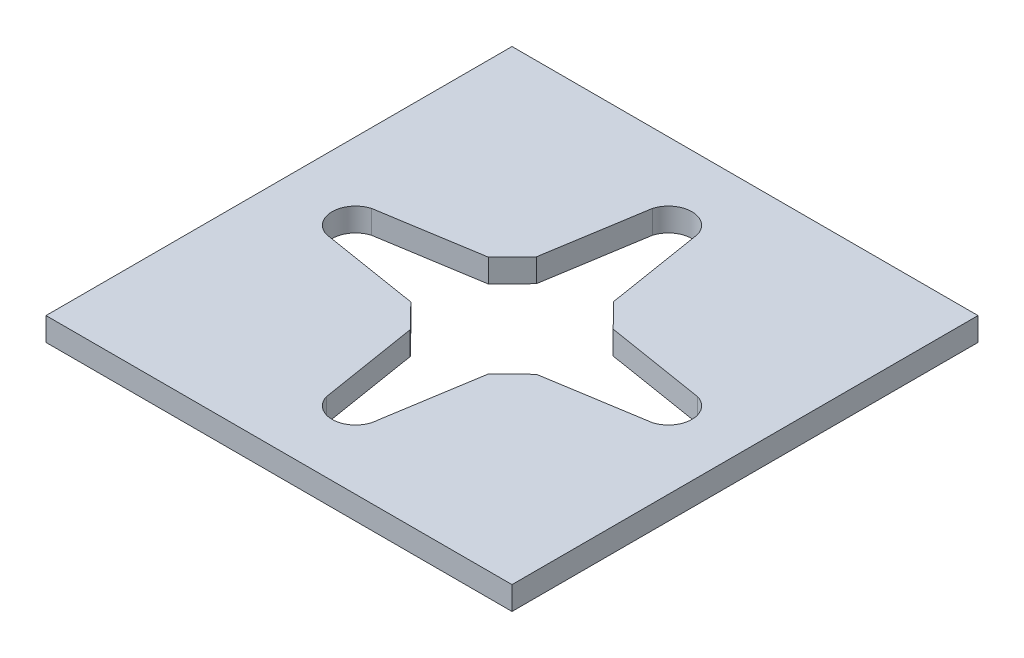
SolidWorks part; units mm, degrees
ref_plane "Front Plane" through (0, 0, 0) normal (0, 0, 1) x (1, 0, 0)
ref_plane "Top Plane" through (0, 0, 0) normal (0, 1, 0) x (1, 0, 0)
ref_plane "Right Plane" through (0, 0, 0) normal (1, 0, 0) x (0, 0, -1)
sketch "Sketch1" plane through (0, 0, 0) normal (0, 1, 0) x (1, 0, 0)
  line L1 (-25.4, -25.4) -> (25.4, -25.4)
  line L2 (-25.4, -25.4) -> (-25.4, 25.4)
  line L3 (-25.4, 25.4) -> (25.4, 25.4)
  line L4 (25.4, -25.4) -> (25.4, 25.4)
  line L5 (-25.4, -25.4) -> (25.4, 25.4) construction
  line L6 (-25.4, 25.4) -> (25.4, -25.4) construction
  point P0 (0, 0)
  dimension "D1" = 50.8
  dimension "D2" = 50.8
extrude "Boss-Extrude1" add sketch "Sketch1" along normal blind 2.54
sketch "Sketch2" plane through (0, 0, 0) normal (0, -1, 0) x (1, 0, 0)
  line L0 (-4.0545, 0.1789) -> (4.1497, 0.1789) construction
  line L1 (-4.2146, 6.8775) -> (-6.7998, 4.2271)
  line L2 (6.8775, 4.2146) -> (17.7568, 2.4618)
  line L3 (4.2271, 6.7998) -> (6.8775, 4.2146)
  line L4 (6.7998, -4.2271) -> (4.2146, -6.8775)
  line L5 (-6.7998, -4.2271) -> (-4.2146, -6.8775)
  line L6 (4.2271, 6.7998) -> (2.5588, 17.155)
  line L7 (-6.7998, 4.2271) -> (-17.7568, 2.4618)
  line L8 (-4.2146, 6.8775) -> (-2.4618, 17.7568)
  line L9 (6.7998, -4.2271) -> (17.7568, -2.4618)
  line L10 (4.2146, -6.8775) -> (2.4618, -17.7568)
  line L11 (-4.2146, -6.8775) -> (-2.4618, -17.7568)
  line L12 (-6.7998, -4.2271) -> (-17.7568, -2.4618)
  circle A5 centre (0, 0) radius 19.558
  arc A9 (2.5556, 17.2157) -> (-2.4618, 17.7568) centre (0, 17.0515) ccw
  arc A10 (17.7568, 2.4618) -> (17.7568, -2.4618) centre (17.0515, 0) cw
  arc A12 (-2.4618, -17.7568) -> (2.4618, -17.7568) centre (0, -17.0515) ccw
  arc A14 (-17.7568, 2.4618) -> (-17.7568, -2.4618) centre (-17.0515, 0) ccw
  arc A15 (2.5556, 17.2157) -> (2.5588, 17.155) centre (0, 17.0515) cw
  point P6 (0, 0)
  point P14 (0, 0)
  dimension "D2" = 39.116
  dimension "D1" = 8.2042
extrude "Cut-Extrude2" cut sketch "Sketch2" against normal blind 2.54 contours L7 A14 L12 L5 L11 A12 L10 L4 L9 A10 L2 L3 L6 A15 A9 L8 L1
